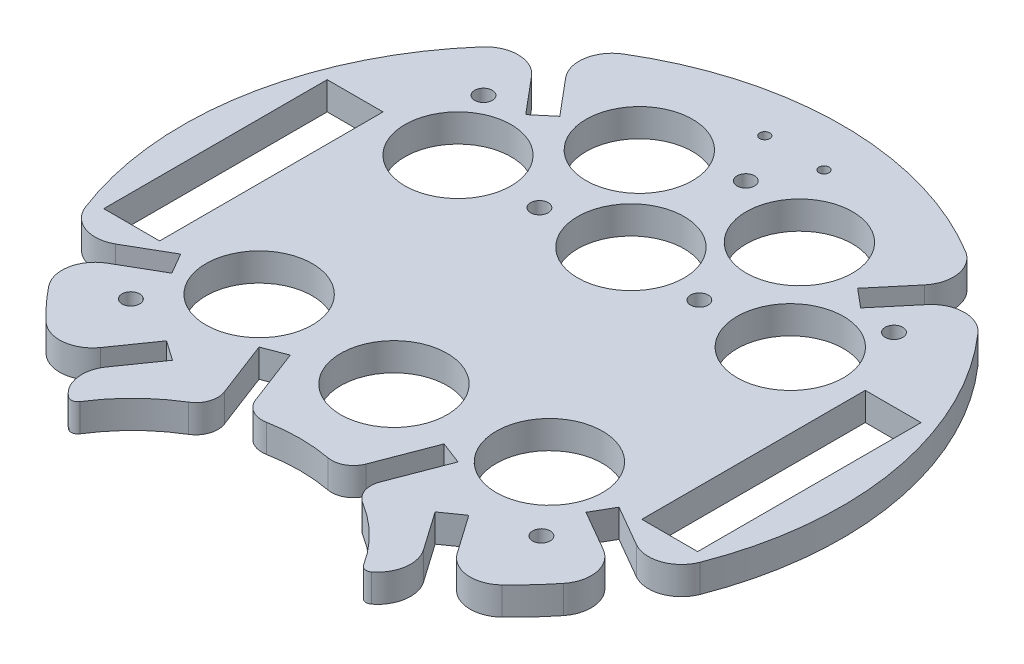
SolidWorks part; units mm, degrees
ref_plane "Front Plane" through (0, 0, 0) normal (0, 0, 1) x (1, 0, 0)
ref_plane "Top Plane" through (0, 0, 0) normal (0, 1, 0) x (1, 0, 0)
ref_plane "Right Plane" through (0, 0, 0) normal (1, 0, 0) x (0, 0, -1)
sketch "Sketch1" plane through (0, 0, 0) normal (0, 1, 0) x (1, 0, 0)
  line L0 (0, 0) -> (-32.9956, -67.352) construction
  line L1 (0, 86.2583) -> (0, -96.8543) construction
  line L2 (0, 0) -> (32.9956, -67.352) construction
  line L3 (-32.9956, -67.352) -> (0, -86.402) construction
  line L4 (32.9956, -67.352) -> (0, -86.402) construction
  line L5 (0, 0) -> (-13.6167, -50.8184) construction
  line L6 (0, 0) -> (-43.0182, -61.4364) construction
  line L7 (0, 0) -> (-48.2091, 57.4533) construction
  line L8 (-83.3992, 0) -> (107.0959, 0) construction
  line L9 (54.8141, -25.4) -> (54.8141, 25.4)
  line L10 (-67.5141, -25.4) -> (-54.8141, -25.4)
  line L11 (-67.5141, -25.4) -> (-67.5141, 25.4)
  line L12 (-67.5141, 25.4) -> (-54.8141, 25.4)
  line L13 (-54.8141, 25.4) -> (-54.8141, -25.4)
  line L14 (67.5141, 25.4) -> (54.8141, 25.4)
  line L15 (67.5141, -25.4) -> (67.5141, 25.4)
  line L16 (67.5141, -25.4) -> (54.8141, -25.4)
  line L17 (0, 0) -> (13.6167, -50.8184) construction
  line L18 (-64.9519, -37.5) -> (0, 0) construction
  line L19 (0, 0) -> (48.2091, 57.4533) construction
  line L20 (0, 0) -> (43.0182, -61.4364) construction
  line L21 (64.9519, -37.5) -> (0, 0) construction
  line L22 (-40.1627, -62.1527) -> (-39.9022, -61.7807)
  line L23 (-34.3581, -44.2739) -> (-40.5201, -53.0742)
  line L24 (44.9916, 49.3407) -> (38.0699, 41.0917)
  line L26 (-29.8527, -47.4286) -> (-36.0148, -56.2289)
  line L27 (-59.208, -31.0083) -> (-49.8282, -25.5929)
  line L30 (-44.668, -58.998) -> (-44.6824, -59.0187)
  line L31 (-56.458, -35.7715) -> (-47.0782, -30.356)
  line L32 (-40.7784, 52.876) -> (-33.8566, 44.627)
  line L34 (40.7784, 52.876) -> (33.8566, 44.627)
  line L35 (56.458, -35.7715) -> (47.0782, -30.356)
  line L36 (-44.9916, 49.3407) -> (-38.0699, 41.0917)
  line L37 (59.208, -31.0083) -> (49.8282, -25.5929)
  line L40 (34.3581, -44.2739) -> (40.5201, -53.0742)
  line L41 (29.8527, -47.4286) -> (36.0148, -56.2289)
  line L42 (-13.6167, -50.8184) -> (-2.8571, -46.701) construction
  line L43 (17.721, -47.7876) -> (22.6182, -34.9901)
  line L44 (-12.4041, -46.2927) -> (-17.4815, -33.0244)
  line L45 (-13.6167, -50.8184) -> (-17.7255, -40.0812) construction
  line L46 (-17.721, -47.7876) -> (-22.6182, -34.9901)
  line L49 (12.4041, -46.2927) -> (17.4815, -33.0244)
  line L50 (-34.3581, -44.2739) -> (-29.8527, -47.4286)
  line L51 (-49.8282, -25.5929) -> (-47.0782, -30.356)
  line L52 (-22.6182, -34.9901) -> (-17.4815, -33.0244)
  line L53 (17.4815, -33.0244) -> (22.6182, -34.9901)
  line L54 (34.3581, -44.2739) -> (29.8527, -47.4286)
  line L55 (49.8282, -25.5929) -> (47.0782, -30.356)
  line L56 (33.8566, 44.627) -> (38.0699, 41.0917)
  line L57 (-38.0699, 41.0917) -> (-33.8566, 44.627)
  arc A0 (-56.3744, 49.4664) -> (-69.893, -27.2023) centre (0, 0) ccw
  arc A1 (-19.7932, -53.8469) -> (-32.2407, -66.1006) centre (0, -86.402) ccw
  arc A2 (38.9256, 64.1077) -> (-38.9256, 64.1077) centre (0, 0) ccw
  arc A3 (56.3744, 49.4664) -> (44.9543, 49.2959) centre (50.737, 44.5198) ccw
  arc A4 (-56.3744, 49.4664) -> (-44.9543, 49.2959) centre (-50.737, 44.5198) cw
  arc A5 (-69.893, -27.2023) -> (-59.0997, -30.9458) centre (-62.9037, -24.4821) ccw
  arc A6 (-51.8486, -54.1915) -> (-40.5201, -53.0742) centre (-46.6637, -48.7724) ccw
  arc A7 (-38.9256, 64.1077) -> (-40.7407, 52.8315) centre (-35.033, 57.6969) ccw
  arc A8 (-58.5044, -46.928) -> (-56.3497, -35.7089) centre (-52.654, -42.2352) cw
  arc A9 (-34.4197, -66.4939) -> (-36.0148, -56.2289) centre (-29.8711, -60.5307) cw
  arc A10 (38.9256, 64.1077) -> (40.7407, 52.8315) centre (35.033, 57.6969) cw
  arc A11 (58.5044, -46.928) -> (56.3497, -35.7089) centre (52.654, -42.2352) ccw
  arc A12 (69.893, -27.2023) -> (59.0997, -30.9458) centre (62.9037, -24.4821) cw
  arc A13 (34.4197, -66.4939) -> (36.0148, -56.2289) centre (29.8711, -60.5307) ccw
  arc A14 (51.8486, -54.1915) -> (40.5201, -53.0742) centre (46.6637, -48.7724) cw
  arc A15 (-58.5044, -46.928) -> (-51.8486, -54.1915) centre (0, 0) ccw
  arc A16 (-33.1901, -67.2563) -> (-32.9956, -67.352) centre (0, 0) ccw
  arc A17 (51.8486, -54.1915) -> (58.5044, -46.928) centre (0, 0) ccw
  arc A18 (69.893, -27.2023) -> (56.3744, 49.4664) centre (0, 0) ccw
  arc A19 (-19.7932, -53.8469) -> (-17.721, -47.7876) centre (-22.3908, -49.5745) ccw
  arc A20 (-6.9964, -48.9499) -> (-12.5843, -45.8219) centre (-7.9145, -44.0349) cw
  arc A21 (19.7932, -53.8469) -> (17.721, -47.7876) centre (22.3908, -49.5745) cw
  arc A22 (6.9964, -48.9499) -> (12.5843, -45.8219) centre (7.9145, -44.0349) ccw
  arc A23 (6.9964, -48.9499) -> (-6.9964, -48.9499) centre (0, -86.402) ccw
  arc A24 (32.2407, -66.1006) -> (19.7932, -53.8469) centre (0, -86.402) ccw
  circle A25 centre (-18.179, 24.3106) radius 2
  circle A26 centre (-32.9956, -24.5929) radius 12.095
  circle A27 centre (32.9956, -24.5929) radius 12.095
  circle A28 centre (37.7724, 25.4) radius 12.095
  circle A29 centre (-37.7724, 25.4) radius 12.075
  circle A30 centre (-18.1963, 47.0458) radius 12.095
  circle A31 centre (18.1963, 47.0458) radius 12.095
  circle A33 centre (0, 26.9383) radius 12.095
  circle A35 centre (0, -26.9383) radius 12.095
  circle A38 centre (-46.6637, -40.0812) radius 2
  circle A39 centre (46.6637, -40.0812) radius 2
  circle A40 centre (46.6637, 40.0812) radius 2
  circle A41 centre (-46.6637, 40.0812) radius 2
  arc A42 (-34.4197, -66.4939) -> (-32.2407, -66.1006) centre (-33.51, -65.3013) ccw
  arc A43 (34.4197, -66.4939) -> (32.2407, -66.1006) centre (33.51, -65.3013) cw
  circle A44 centre (-6.731, 64.1077) radius 1.143
  circle A45 centre (6.731, 64.1077) radius 1.143
  circle A47 centre (18.179, 24.3106) radius 2
  circle A48 centre (0, 53.0612) radius 2
  point P14 (-62.6039, 0)
  point P23 (62.6039, 0)
  point P35 (-31.5178, -45.012)
  point P40 (-46.7211, -26.9744)
  point P45 (-34.6777, 41.3272)
  point P122 (-29.8711, 0)
  dimension "D1" = 150
  dimension "D3" = 120
  dimension "D2" = 76.2
  dimension "D10" = 5.5
  dimension "D15" = 13.462
  dimension "D18" = 2.286
  dimension "D12" = 4
  dimension "D4" = 50.8
  dimension "D5" = 12.7
  dimension "D6" = 80
  dimension "D7" = 80
  dimension "D8" = 25
  dimension "D9" = 30
extrude "Boss-Extrude1" add sketch "Sketch1" along normal blind 6.35
